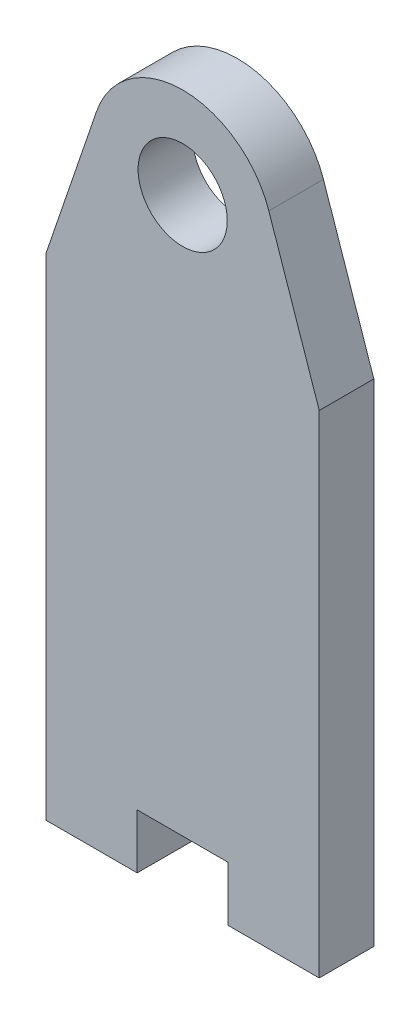
SolidWorks part; units mm, degrees
ref_plane "Alzado" through (0, 0, 0) normal (0, 0, 1) x (1, 0, 0)
ref_plane "Planta" through (0, 0, 0) normal (0, 1, 0) x (1, 0, 0)
ref_plane "Vista lateral" through (0, 0, 0) normal (1, 0, 0) x (0, 0, -1)
sketch "Model" plane through (0, 0, 0) normal (0, 0, 1) x (1, 0, 0)
  line L0 (21.4055, 24.45) -> (21.4055, -2.55)
  line L1 (36.4055, 24.45) -> (36.4055, -2.55)
  line L2 (36.4055, -2.55) -> (31.4055, -2.55)
  line L3 (26.4055, -2.55) -> (21.4055, -2.55)
  line L4 (26.4055, 0.45) -> (26.4055, -2.55)
  line L5 (31.4055, 0.45) -> (26.4055, 0.45)
  line L6 (31.4055, -2.55) -> (31.4055, 0.45)
  line L7 (33.6378, 32.5642) -> (36.4055, 24.45)
  line L8 (21.4055, 24.45) -> (24.1732, 32.5642)
  circle A0 centre (28.9041, 30.95) radius 2.45
  arc A1 (33.6378, 32.5642) -> (24.1732, 32.5642) centre (28.9055, 30.95) ccw
extrude "Saliente-Extruir1" add sketch "Model" along normal blind 3
